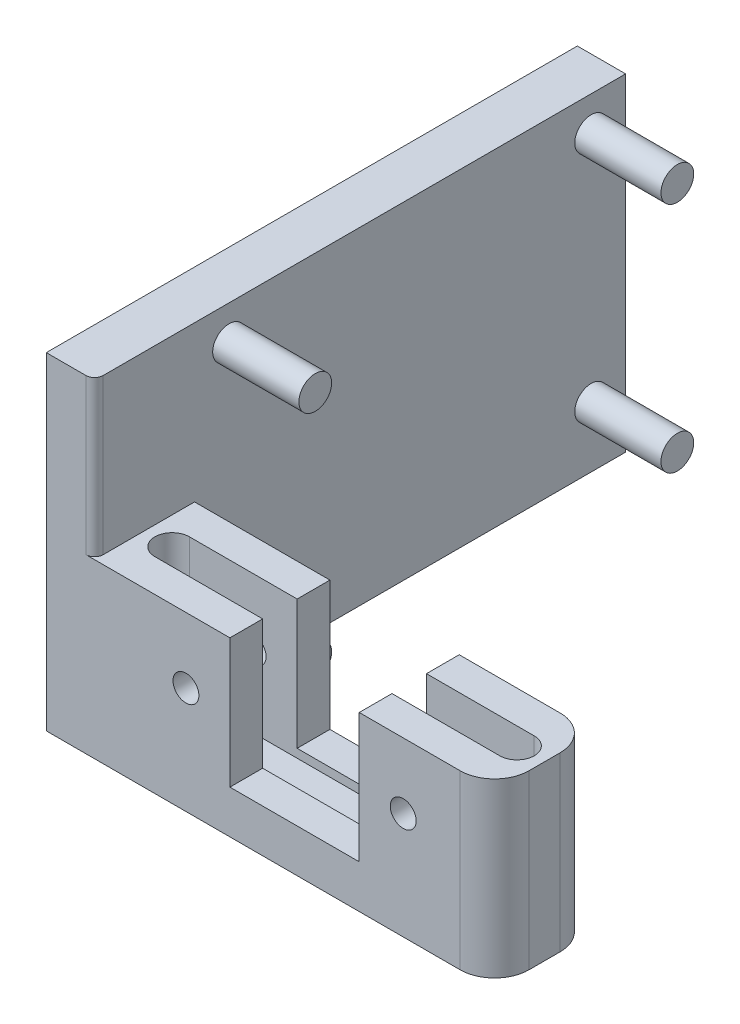
SolidWorks part; units mm, degrees
ref_plane "前视" through (0, 0, 0) normal (0, 0, 1) x (1, 0, 0)
ref_plane "上视" through (0, 0, 0) normal (0, 1, 0) x (1, 0, 0)
ref_plane "右视" through (0, 0, 0) normal (1, 0, 0) x (0, 0, -1)
sketch "草图1" plane through (0, 0, 0) normal (0, 1, 0) x (1, 0, 0)
  line L0 (-5.22, 18.4025) -> (-2.42, 18.4025)
  line L1 (-2.42, 18.4025) -> (-2.42, -6.5975)
  line L2 (-2.42, -6.5975) -> (20.78, -6.5975)
  line L3 (20.78, -6.5975) -> (20.78, -12.3975)
  line L4 (20.78, -12.3975) -> (-5.22, -12.3975)
  line L5 (-5.22, -12.3975) -> (-5.22, 18.4025)
  dimension "D1" = 5.8
  dimension "D2" = 26
  dimension "D3" = 30.8
  dimension "D4" = 2.8
extrude "凸台-拉伸1" add sketch "草图1" along normal blind 19
sketch "草图3" plane through (0, 0, 12.3975) normal (0, 0, 1) x (1, 0, 0)
  line L2 (20.78, 19) -> (-2.42, 19)
  line L3 (20.78, 19) -> (20.78, 10)
  line L5 (20.78, 10) -> (-2.42, 10)
  line L6 (-2.42, 19) -> (-2.42, 10)
  dimension "D1" = 23.2
  dimension "D2" = 9
extrude "切除-拉伸2" cut sketch "草图3" against normal through all
sketch "草图4" plane through (0, 10, 0) normal (0, 1, 0) x (1, 0, 0)
  line L0 (3.6992, -9.4975) -> (13.842, -9.4975) construction
  line L2 (-2.42, -6.5975) -> (20.78, -6.5975) construction
  line L3 (9.18, -7.9821) -> (9.18, -10.8799) construction
  line L4 (20.78, -6.5975) -> (20.78, -12.3975) construction
  line L5 (-0.82, -9.4975) -> (19.18, -9.4975) construction
  line L6 (-0.82, -8.4975) -> (19.18, -8.4975)
  line L7 (-0.82, -10.4975) -> (19.18, -10.4975)
  arc A0 (-0.82, -8.4975) -> (-0.82, -10.4975) centre (-0.82, -9.4975) ccw
  arc A1 (19.18, -10.4975) -> (19.18, -8.4975) centre (19.18, -9.4975) ccw
  point P10 (9.18, -9.4975)
  dimension "D2" = 11.6
  dimension "D1" = 2.9
extrude "切除-拉伸3" cut sketch "草图4" against normal blind 8
sketch "草图5" plane through (0, 0, 12.3975) normal (0, 0, 1) x (1, 0, 0)
  line L0 (-2.42, 10) -> (20.78, 10) construction
  line L1 (12.93, 2.5) -> (5.43, 2.5)
  line L2 (12.93, 2.5) -> (12.93, 10)
  line L3 (12.93, 10) -> (5.43, 10)
  line L4 (5.43, 2.5) -> (5.43, 10)
  line L5 (12.93, 2.5) -> (5.43, 10) construction
  line L6 (12.93, 10) -> (5.43, 2.5) construction
  line L7 (20.78, 10) -> (20.78, 0) construction
  point P0 (9.18, 6.25)
  dimension "D1" = 7.5
  dimension "D2" = 11.6
  dimension "D3" = 7.5
extrude "切除-拉伸4" cut sketch "草图5" against normal through all
sketch "草图7" plane through (0, 0, 12.3975) normal (0, 0, 1) x (1, 0, 0)
  line L0 (5.43, 10) -> (5.43, 2.5) construction
  line L1 (12.93, 2.5) -> (12.93, 10) construction
  line L2 (-2.42, 10) -> (5.43, 10) construction
  line L3 (12.93, 10) -> (20.78, 10) construction
  circle A0 centre (2.88, 6.2) radius 0.75
  circle A1 centre (15.48, 6.2) radius 0.75
  point P6 (12.93, 6.25)
  dimension "D1" = 1.5
  dimension "D2" = 1.5
  dimension "D3" = 2.55
  dimension "D4" = 2.55
  dimension "D5" = 3.8
  dimension "D6" = 3.8
extrude "切除-拉伸6" cut sketch "草图7" against normal through all
fillet "圆角3" radius 2 2 edges at (20.78, 5, 12.3975) (20.78, 5, 6.5975)
fillet "圆角4" radius 0.5 1 edges at (-2.42, 14.5, 12.3975)
sketch "草图8" plane through (-2.42, 0, 0) normal (1, 0, 0) x (0, 0, -1)
  line L0 (18.4025, 19) -> (18.4025, 0) construction
  line L1 (-11.8975, 19) -> (18.4025, 19) construction
  circle A0 centre (16.4025, 17) radius 0.95
  circle A1 centre (16.4025, 3.5) radius 0.95
  circle A2 centre (-4.5975, 3.5) radius 0.95
  circle A3 centre (-4.5975, 17) radius 0.95
  dimension "D1" = 1.9
  dimension "D2" = 1.9
  dimension "D3" = 1.9
  dimension "D4" = 1.9
  dimension "D5" = 2
  dimension "D6" = 2
  dimension "D7" = 2
  dimension "D8" = 13.5
  dimension "D9" = 2
  dimension "D10" = 13.5
  dimension "D11" = 21
  dimension "D12" = 21
extrude "凸台-拉伸2" add sketch "草图8" along normal blind 5
